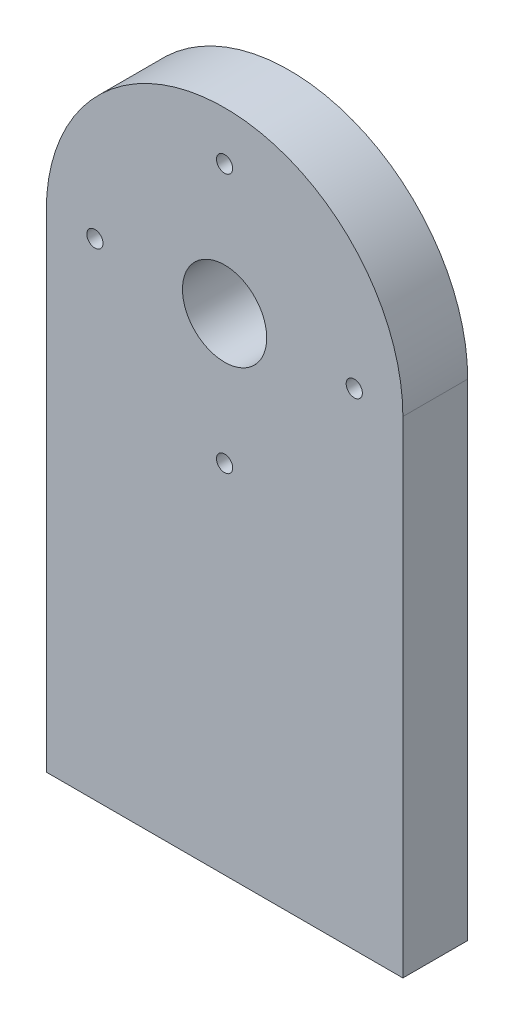
SolidWorks part; units mm, degrees
ref_plane "Front Plane" through (0, 0, 0) normal (0, 0, 1) x (1, 0, 0)
ref_plane "Top Plane" through (0, 0, 0) normal (0, 1, 0) x (1, 0, 0)
ref_plane "Right Plane" through (0, 0, 0) normal (1, 0, 0) x (0, 0, -1)
sketch "Sketch1" plane through (0, 0, 0) normal (0, 0, 1) x (1, 0, 0)
  line L0 (-57.2515, 0) -> (52.7485, 0)
  line L1 (52.7485, 0) -> (52.7485, 150)
  line L2 (-57.2515, 0) -> (-57.2515, 150)
  arc A0 (-57.2515, 150) -> (52.7485, 150) centre (-2.2515, 150) cw
  circle A2 centre (-2.2515, 150) radius 13
  dimension "D4" = 26
  dimension "D1" = 110
  dimension "D2" = 150
  dimension "D3" = 150
extrude "Boss-Extrude1" add sketch "Sketch1" along normal blind 20
sketch "Sketch3" plane through (0, 0, 20) normal (0, 0, 1) x (1, 0, 0)
  circle A0 centre (-2.2515, 150) radius 40 construction
  point P3 (-2.2515, 190)
  point P4 (37.7485, 150)
  point P5 (-2.2515, 110)
  point P6 (-42.2515, 150)
  dimension "D1" = 80
hole_wizard "Ø5.0mm Dowel Hole1" positions "3DSketch1" profile "Sketch4" hole size "Ø5.0" standard "ANSI Metric" end condition through all
sketch3d "3DSketch1"
  point P0 (-2.2515, 190, 20)
  point P3 (37.7485, 150, 20)
  point P6 (-2.2515, 110, 20)
  point P9 (-42.2515, 150, 20)
sketch "Sketch4" plane through (-2.2515, 190, 20) normal (1, 0, 0) x (0, -1, 0)
  line L0 (0, 0) -> (0, 20)
  line L1 (0, 20) -> (2.5, 20)
  line L2 (2.5, 20) -> (2.5, 0)
  line L5 (2.5, 0) -> (0, 0)
  line L11 (0, -6.35) -> (0, 107.95) construction
  dimension "Thru Hole Dia." = 5
  dimension "Thru Hole Depth" = 20
sketch "Sketch5" plane through (0, 0, 0) normal (0, -1, 0) x (-1, 0, 0)
  line L0 (57.2515, -20) -> (57.2515, 0) construction
  line L1 (-52.7485, -20) -> (-52.7485, 0) construction
  line L2 (57.2515, -20) -> (-52.7485, -20) construction
  point P0 (42.2515, -10)
  point P1 (-37.7485, -10)
  dimension "D1" = 15
  dimension "D2" = 15
  dimension "D3" = 10
hole_wizard "Ø5.0mm Dowel Hole2" positions "3DSketch2" profile "Sketch6" hole size "Ø5.0" standard "ANSI Metric"
sketch3d "3DSketch2"
  point P0 (-42.2515, 0, 10)
  point P3 (37.7485, 0, 10)
sketch "Sketch6" plane through (-42.2515, 0, 10) normal (1, 0, 0) x (0, 0, -1)
  line L0 (0, 0) -> (0, 147.5)
  line L1 (0, 147.5) -> (2.5, 147.5)
  line L2 (2.5, 147.5) -> (2.5, 0)
  line L5 (2.5, 0) -> (0, 0)
  line L11 (0, -6.35) -> (0, 107.95) construction
  dimension "Thru Hole Dia." = 5
  dimension "Thru Hole Depth" = 147.5
